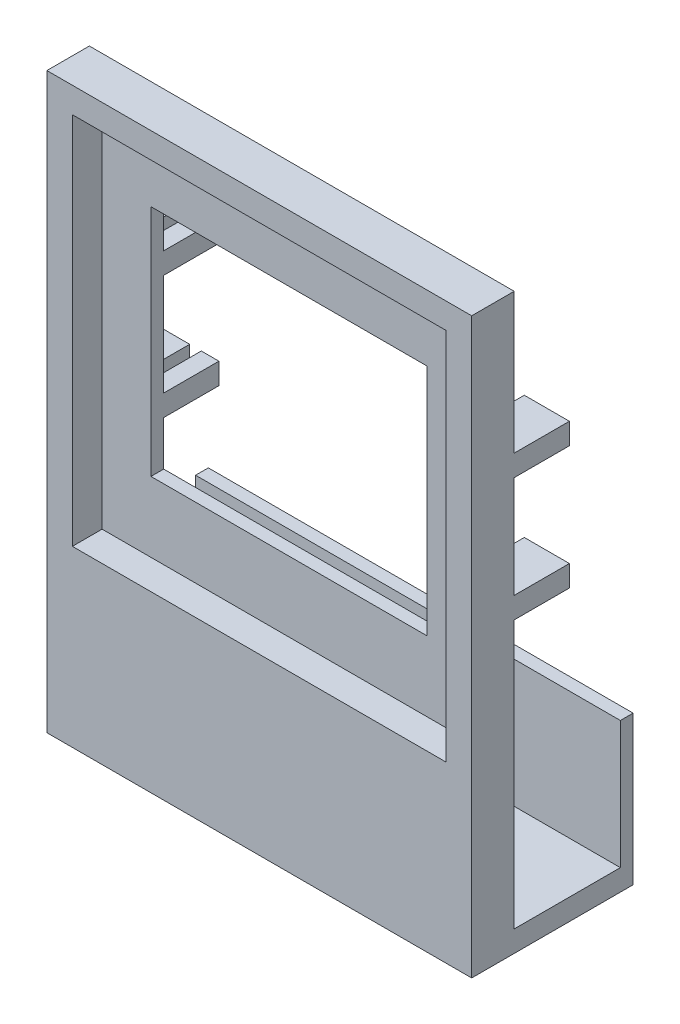
SolidWorks part; units mm, degrees
ref_plane "前视基准面" through (0, 0, 0) normal (0, 0, 1) x (1, 0, 0)
ref_plane "上视基准面" through (0, 0, 0) normal (0, 1, 0) x (1, 0, 0)
ref_plane "右视基准面" through (0, 0, 0) normal (1, 0, 0) x (0, 0, -1)
sketch "草图1" plane through (0, 0, 0) normal (0, 0, 1) x (1, 0, 0)
  line L1 (-50, 50) -> (50, 50)
  line L2 (-50, 50) -> (-50, -50)
  line L3 (-50, -50) -> (50, -50)
  line L4 (50, 50) -> (50, -50)
  line L5 (-50, 50) -> (50, -50) construction
  line L6 (-50, -50) -> (50, 50) construction
  point P0 (0, 0)
  dimension "D1" = 100
  dimension "D2" = 100
extrude "凸台-拉伸1" add sketch "草图1" along normal blind 10
sketch "草图2" plane through (0, 0, 10) normal (0, 0, 1) x (1, 0, 0)
  line L1 (-32.5, 27.5) -> (32.5, 27.5)
  line L2 (-32.5, 27.5) -> (-32.5, -27.5)
  line L3 (-32.5, -27.5) -> (32.5, -27.5)
  line L4 (32.5, 27.5) -> (32.5, -27.5)
  line L5 (-32.5, 27.5) -> (32.5, -27.5) construction
  line L6 (-32.5, -27.5) -> (32.5, 27.5) construction
  point P0 (0, 0)
  dimension "D1" = 55
  dimension "D2" = 65
extrude "切除-拉伸1" cut sketch "草图2" against normal through all
sketch "草图3" plane through (0, 0, 10) normal (0, 0, 1) x (1, 0, 0)
  line L1 (-44, 44) -> (44, 44)
  line L2 (-44, 44) -> (-44, -44)
  line L3 (-44, -44) -> (44, -44)
  line L4 (44, 44) -> (44, -44)
  line L5 (-44, 44) -> (44, -44) construction
  line L6 (-44, -44) -> (44, 44) construction
  point P0 (0, 0)
  dimension "D1" = 88
  dimension "D2" = 88
extrude "切除-拉伸2" cut sketch "草图3" against normal blind 7
sketch "草图4" plane through (0, -50, 0) normal (0, -1, 0) x (1, 0, 0)
  line L1 (50, -28) -> (-50, -28)
  line L2 (50, -28) -> (50, 10)
  line L3 (50, 10) -> (-50, 10)
  line L4 (-50, -28) -> (-50, 10)
  line L5 (50, -28) -> (-50, 10) construction
  line L6 (50, 10) -> (-50, -28) construction
  line L7 (-50, 10) -> (50, 10) construction
  dimension "D1" = 38
extrude "凸台-拉伸2" add sketch "草图4" along normal blind 35
sketch "草图8" plane through (0, -50, 0) normal (0, 1, 0) x (1, 0, 0)
  line L0 (50, 0) -> (50, 25)
  line L1 (50, 28) -> (50, 0) construction
  line L2 (50, 0) -> (-50, 0)
  line L3 (-50, 0) -> (-50, 25)
  line L4 (-50, 0) -> (-50, 28) construction
  line L5 (-50, 25) -> (50, 25)
  dimension "D1" = 25
extrude "切除-拉伸3" cut sketch "草图8" against normal blind 30
sketch "草图9" plane through (0, 0, 0) normal (0, 0, -1) x (-1, 0, 0)
  line L0 (-50, 0) -> (50, 0) construction
  line L1 (-50, -80) -> (-50, 50) construction
  line L2 (50, 50) -> (50, -80) construction
  line L3 (50, 0) -> (50, 17)
  line L4 (50, 0) -> (50, -17)
  line L5 (0, 50) -> (0, -27.5) construction
  line L6 (-50, 50) -> (50, 50) construction
  line L7 (32.5, -27.5) -> (-32.5, -27.5) construction
  line L8 (-50, 0) -> (-50, -17)
  line L9 (-50, 0) -> (-50, 17)
  line L10 (50, 17) -> (50, 12)
  line L11 (50, 12) -> (32.5, 12)
  line L12 (32.5, 27.5) -> (32.5, -27.5) construction
  line L13 (32.5, 12) -> (32.5, 17)
  line L14 (32.5, 17) -> (50, 17)
  line L15 (50, -17) -> (32.5, -17)
  line L16 (32.5, -17) -> (32.5, -12)
  line L17 (32.5, -12) -> (50, -12)
  line L18 (50, -12) -> (50, -17)
  line L19 (-50, -17) -> (-32.5, -17)
  line L20 (-32.5, -17) -> (-32.5, -12)
  line L21 (-32.5, -12) -> (-50, -12)
  line L22 (-50, 12) -> (-32.5, 12)
  line L23 (-32.5, 12) -> (-32.5, 17)
  line L24 (-32.5, 17) -> (-50, 17)
  line L25 (-50, 12) -> (-50, 17)
  line L26 (-50, -12) -> (-50, -17)
  point P17 (-50, -12)
  point P29 (-50, 12)
  line M11 (-32.5, -27.5) -> (-32.5, 27.5)
  line M13 (32.5, 27.5) -> (32.5, -27.5)
  line M14 (-50, 50) -> (-50, -80)
  line M16 (50, -80) -> (50, 50)
  dimension "D1" = 17
  dimension "D2" = 17
  dimension "D3" = 5
  dimension "D4" = 5
extrude "凸台-拉伸3" add sketch "草图9" along normal blind 13 contours L24 L22 M11 M14 | L21 L8 L19 M11 | L14 L11 L3 M13 | L17 L15 M13 M16
sketch "草图10" plane through (0, 0, -13) normal (0, 0, -1) x (-1, 0, 0)
  line L0 (32.5, 17) -> (36.6514, 17)
  line L1 (32.5, 17) -> (50, 17) construction
  line L2 (36.6514, 17) -> (39.3848, 17)
  line L3 (39.3848, 17) -> (39.3848, 12)
  line L4 (50, 12) -> (32.5, 12) construction
  line L5 (39.3848, 12) -> (36.6514, 12)
  line L6 (36.6514, 12) -> (36.6514, 17)
  line L7 (0, 0) -> (0, 50000) construction
  line L8 (-1000, 0) -> (49000, 0) construction
  line L9 (-39.3848, 12) -> (-36.6514, 12)
  line L10 (-39.3848, 17) -> (-39.3848, 12)
  line L11 (-36.6514, 12) -> (-36.6514, 17)
  line L12 (-36.6514, 17) -> (-39.3848, 17)
  line L13 (39.3848, -12) -> (36.6514, -12)
  line L14 (36.6514, -12) -> (36.6514, -17)
  line L15 (39.3848, -17) -> (39.3848, -12)
  line L16 (36.6514, -17) -> (39.3848, -17)
  line L17 (-39.3848, -12) -> (-36.6514, -12)
  line L18 (-39.3848, -17) -> (-39.3848, -12)
  line L19 (-36.6514, -12) -> (-36.6514, -17)
  line L20 (-36.6514, -17) -> (-39.3848, -17)
  line M11 (50, 17) -> (32.5, 17)
  line M13 (32.5, 12) -> (50, 12)
extrude "切除-拉伸5" cut sketch "草图10" against normal blind 12 contours L11 L12 L10 L9 | L20 L19 L17 L18 | L14 L16 L15 L13 | L6 L3 M13 M11
sketch "草图11" plane through (0, -85, 0) normal (0, -1, 0) x (1, 0, 0)
  line L1 (16.2344, -20.598) -> (-16.2344, -20.598)
  line L2 (16.2344, -20.598) -> (16.2344, -3.926)
  line L3 (16.2344, -3.926) -> (-16.2344, -3.926)
  line L4 (-16.2344, -20.598) -> (-16.2344, -3.926)
  line L5 (16.2344, -20.598) -> (-16.2344, -3.926) construction
  line L6 (16.2344, -3.926) -> (-16.2344, -20.598) construction
  point P0 (0, -12.262)
extrude "切除-拉伸6" cut sketch "草图11" against normal blind 12
